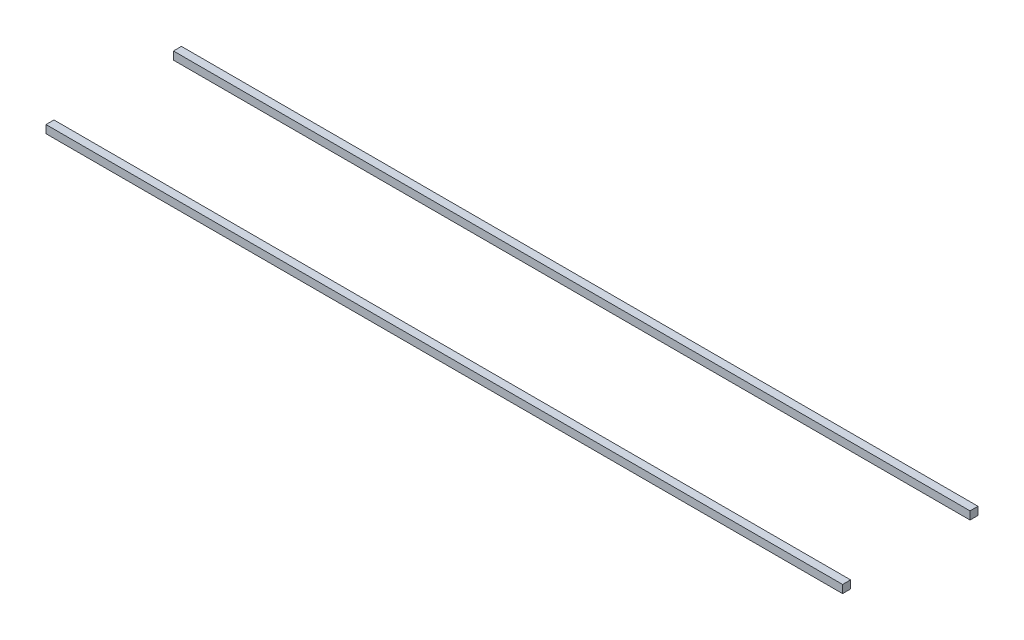
SolidWorks part; units mm, degrees
ref_plane "Plano frontal" through (0, 0, 0) normal (0, 0, 1) x (1, 0, 0)
ref_plane "Plano superior" through (0, 0, 0) normal (0, 1, 0) x (1, 0, 0)
ref_plane "Plano direito" through (0, 0, 0) normal (1, 0, 0) x (0, 0, -1)
sketch "Esboço1" plane through (0, 0, 0) normal (1, 0, 0) x (0, 0, -1)
  line L0 (0, 0) -> (0, 102.027) construction
  line L1 (0, 0) -> (285.4439, 0) construction
  line L2 (-300, 20) -> (-340, -20) construction
  line L3 (300, -20) -> (340, -20)
  line L4 (300, -20) -> (300, 20)
  line L5 (300, 20) -> (340, 20)
  line L6 (340, -20) -> (340, 20)
  line L7 (300, -20) -> (340, 20) construction
  line L8 (300, 20) -> (340, -20) construction
  line L9 (-300, -20) -> (-340, 20) construction
  line L10 (-340, -20) -> (-340, 20)
  line L11 (-300, 20) -> (-340, 20)
  line L12 (-300, -20) -> (-300, 20)
  line L13 (-300, -20) -> (-340, -20)
  point P3 (320, 0)
  point P13 (-320, 0)
  dimension "D1" = 40
  dimension "D2" = 600
extrude "Ressalto-extrusão1" add sketch "Esboço1" along normal blind 4000
